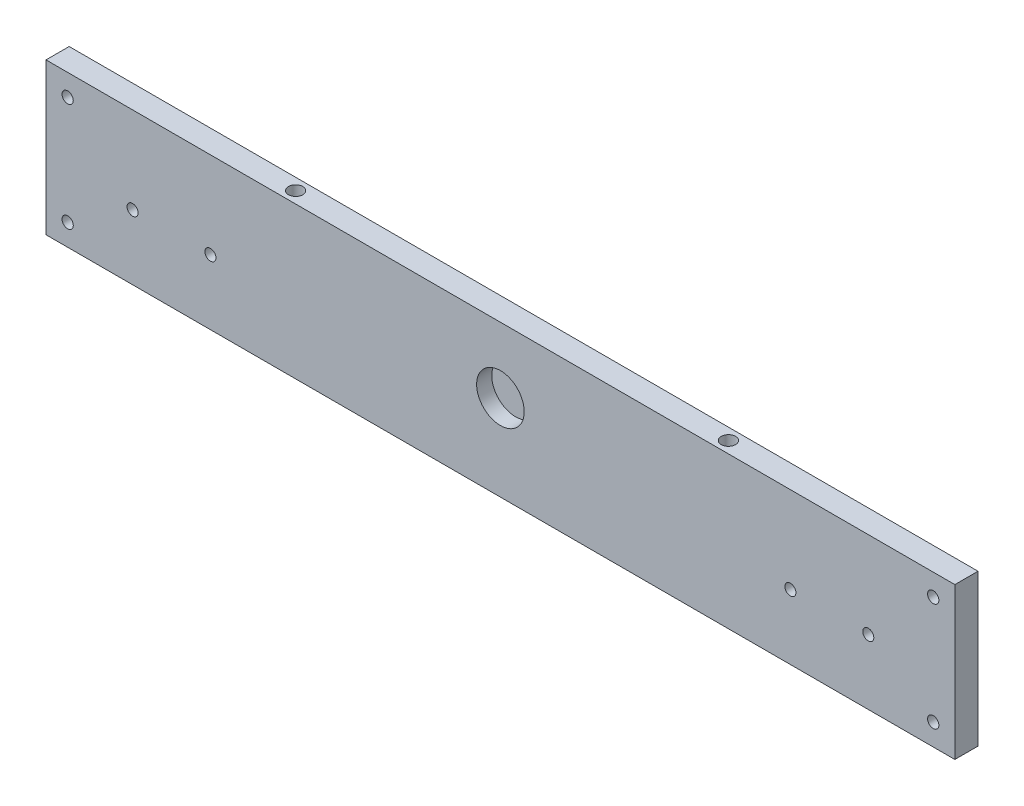
SolidWorks part; units mm, degrees
ref_plane "Plano frontal" through (0, 0, 0) normal (0, 0, 1) x (1, 0, 0)
ref_plane "Plano superior" through (0, 0, 0) normal (0, 1, 0) x (1, 0, 0)
ref_plane "Plano direito" through (0, 0, 0) normal (1, 0, 0) x (0, 0, -1)
sketch "Esboço1" plane through (0, 0, 0) normal (0, 0, 1) x (1, 0, 0)
  line L1 (210, -35) -> (-210, -35)
  line L2 (210, -35) -> (210, 35)
  line L3 (210, 35) -> (-210, 35)
  line L4 (-210, -35) -> (-210, 35)
  line L5 (210, -35) -> (-210, 35) construction
  line L6 (210, 35) -> (-210, -35) construction
  point P0 (0, 0)
  dimension "D1" = 70
  dimension "D2" = 420
extrude "Ressalto-extrusão1" add sketch "Esboço1" along normal blind 10.7
sketch "Esboço5" plane through (0, 0, 10.7) normal (0, 0, 1) x (1, 0, 0)
  line L0 (0, -34.5824) -> (0, 46.0094) construction
  line L1 (-210, -35) -> (210, -35) construction
  circle A0 centre (0, 4.65) radius 11
  dimension "D2" = 22
  dimension "D1" = 39.65
extrude "Corte-extrusão4" cut sketch "Esboço5" against normal blind 7
hole_wizard "Furo roscado para conduíte de #10-321" positions "Esboço8" profile "Esboço7" tap size "#10-32" standard "Helicoil® Inch" end condition through all
sketch "Esboço8" plane through (0, 0, 10.7) normal (0, 0, 1) x (1, 0, 0)
  line L0 (-210, 35) -> (-210, -35) construction
  line L1 (-210, -35) -> (210, -35) construction
  line L2 (0, 48.9445) -> (0, -58.6558) construction
  line L4 (45.2995, 0) -> (-44.2128, 0) construction
  point P0 (-170, -5)
  point P2 (-134, -5)
  point P20 (134, -5)
  point P21 (170, -5)
  dimension "D1" = 40
  dimension "D2" = 30
  dimension "D3" = 36
cosmetic thread "Rosca de furo1" parameters "D1"=15, "D2"=5.936
cosmetic thread "Rosca de furo2" parameters "D1"=15, "D2"=5.936
cosmetic thread "Rosca de furo3" parameters "D1"=15, "D2"=5.936
cosmetic thread "Rosca de furo4" parameters "D1"=15, "D2"=5.936
sketch "Esboço7" plane through (-170, -5, 10.7) normal (1, 0, 0) x (0, -1, 0)
  line L0 (0, 0) -> (0, 10.7)
  line L1 (0, 10.7) -> (2.5527, 10.7)
  line L2 (2.5527, 10.7) -> (2.5527, 0)
  line L5 (2.5527, 0) -> (0, 0)
  line L11 (0, -6.35) -> (0, 107.95) construction
  dimension "Thru Tap Drill Dia." = 5.1054
  dimension "Thru Tap Drill Depth" = 10.7
hole_wizard "Furo roscado para conduíte de M5x0.81" positions "Esboço9" profile "Esboço10" tap size "M5x0.8" standard "Helicoil® Metric" end condition through all
sketch "Esboço9" plane through (0, 0, 10.7) normal (0, 0, 1) x (1, 0, 0)
  line L0 (-210, 35) -> (-210, -35) construction
  line L1 (210, 35) -> (-210, 35) construction
  line L2 (-27.8831, 0) -> (45.0891, 0) construction
  line L4 (0, -51.3145) -> (0, 53.343) construction
  point P0 (-200, 25)
  point P17 (-200, -25)
  point P19 (200, -25)
  point P20 (200, 25)
  dimension "D1" = 10
  dimension "D2" = 10
sketch "Esboço10" plane through (-200, 25, 10.7) normal (1, 0, 0) x (0, -1, 0)
  line L0 (0, 0) -> (0, 10.7)
  line L1 (0, 10.7) -> (2.6, 10.7)
  line L2 (2.6, 10.7) -> (2.6, 0)
  line L5 (2.6, 0) -> (0, 0)
  line L11 (0, -6.35) -> (0, 107.95) construction
  dimension "Thru Tap Drill Dia." = 5.2
  dimension "Thru Tap Drill Depth" = 10.7
cosmetic thread "Rosca de furo5" parameters "D1"=15, "D2"=6.145
cosmetic thread "Rosca de furo6" parameters "D1"=15, "D2"=6.145
cosmetic thread "Rosca de furo7" parameters "D1"=15, "D2"=6.145
cosmetic thread "Rosca de furo8" parameters "D1"=15, "D2"=6.145
hole_wizard "Furo roscado para conduíte de 1/4-281" positions "Esboço11" profile "Esboço12" tap size "1/4-28" standard "Helicoil® Inch"
sketch "Esboço11" plane through (0, 35, 0) normal (0, 1, 0) x (1, 0, 0)
  line L0 (0, 24.6176) -> (0, -36.0013) construction
  line L3 (-210, -10.7) -> (-210, 0) construction
  line L4 (210, 0) -> (-210, 0) construction
  point P0 (-100, -5.35)
  point P16 (100, -5.35)
  dimension "D1" = 110
  dimension "D2" = 5.35
cosmetic thread "Rosca de furo9" parameters "D1"=15, "D2"=7.6073
cosmetic thread "Rosca de furo10" parameters "D1"=15, "D2"=7.6073
sketch "Esboço12" plane through (-100, 35, 5.35) normal (1, 0, 0) x (0, 0, 1)
  line L0 (0, 0) -> (0, 16.9917)
  line L1 (0, 16.9917) -> (3.3147, 15)
  line L2 (3.3147, 15) -> (3.3147, 0)
  line L5 (3.3147, 0) -> (0, 0)
  line L10 (0, 16.9917) -> (-3.3147, 15) construction
  line L11 (0, -6.35) -> (0, 107.95) construction
  dimension "Tap Drill Dia." = 6.6294
  dimension "Tap Drill Depth" = 15
  dimension "Drill Angle" = 118
